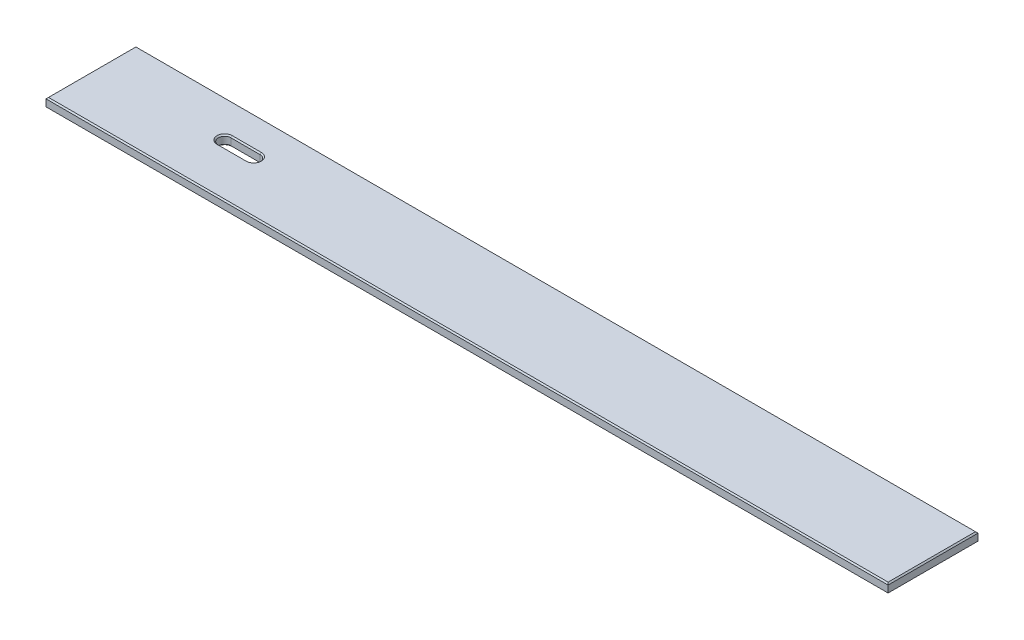
SolidWorks part; units mm, degrees
material "Oak"
ref_plane "Front Plane" through (0, 0, 0) normal (0, 0, 1) x (1, 0, 0)
ref_plane "Top Plane" through (0, 0, 0) normal (0, 1, 0) x (1, 0, 0)
ref_plane "Right Plane" through (0, 0, 0) normal (1, 0, 0) x (0, 0, -1)
sketch "Sketch1" plane through (0, 0, 0) normal (0, 1, 0) x (1, 0, 0)
  line L1 (0, 0) -> (1695.45, 0)
  line L2 (0, 0) -> (0, 180.975)
  line L3 (0, 180.975) -> (1695.45, 180.975)
  line L4 (1695.45, 0) -> (1695.45, 180.975)
  line L6 (254, 118.256) -> (312.7502, 118.256)
  line L8 (254, 92.856) -> (312.7502, 92.856)
  arc A4 (312.7502, 92.856) -> (312.7502, 118.256) centre (312.7502, 105.556) ccw
  arc A5 (254, 118.256) -> (254, 92.856) centre (254, 105.556) ccw
  point P14 (312.7502, 118.256)
  dimension "D7" = 25.4
  dimension "D1" = 180.975
  dimension "D2" = 1695.45
  dimension "D3" = 58.7502
  dimension "D4" = 105.556
  dimension "D5" = 254
extrude "Boss-Extrude1" add sketch "Sketch1" along normal blind 19.05
chamfer "Chamfer1" distance 2.54 angle 45 8 edges at (847.725, 19.05, -180.975) (1695.45, 19.05, -90.4875) (847.725, 19.05, 0) (0, 19.05, -90.4875) (283.3751, 19.05, -118.256) (283.3751, 19.05, -92.856) (241.3, 19.05, -105.556) (325.4502, 19.05, -105.556)
chamfer "Chamfer2" distance 2.54 angle 45 8 edges at (283.3751, 0, -118.256) (283.3751, 0, -92.856) (847.725, 0, 0) (1695.45, 0, -90.4875) (847.725, 0, -180.975) (0, 0, -90.4875) (241.3, 0, -105.556) (325.4502, 0, -105.556)
